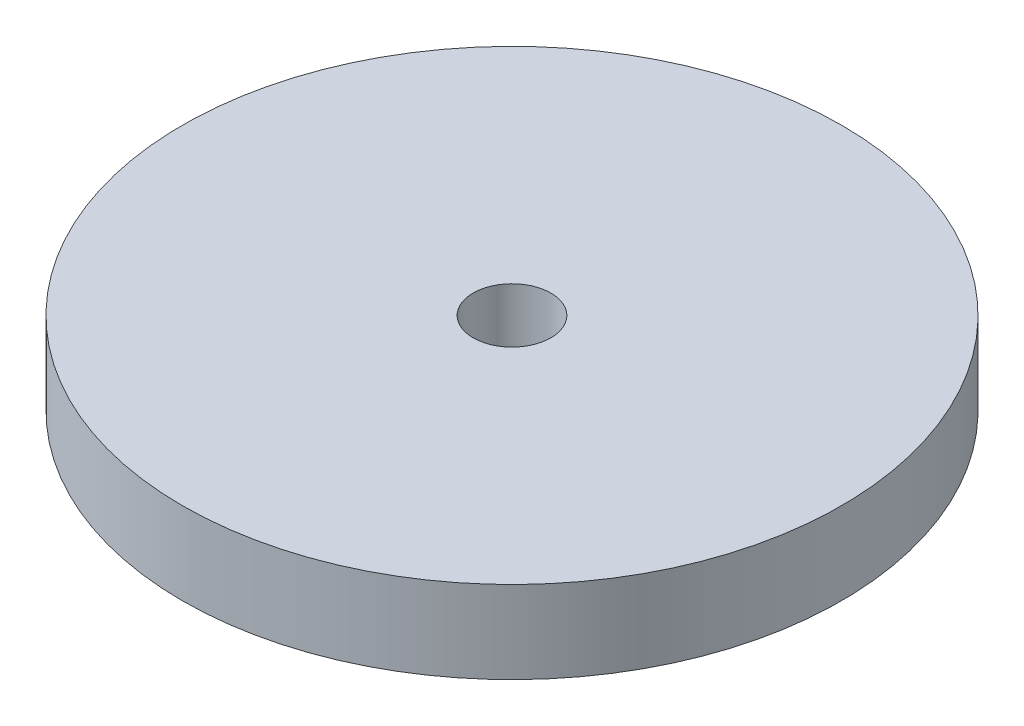
SolidWorks part; units mm, degrees
ref_plane "Front Plane" through (0, 0, 0) normal (0, 0, 1) x (1, 0, 0)
ref_plane "Top Plane" through (0, 0, 0) normal (0, 1, 0) x (1, 0, 0)
ref_plane "Right Plane" through (0, 0, 0) normal (1, 0, 0) x (0, 0, -1)
sketch "Sketch1" plane through (0, 0, 0) normal (0, 1, 0) x (1, 0, 0)
  circle A0 centre (0, 0) radius 14
  dimension "D1" = 28
extrude "Boss-Extrude1" add sketch "Sketch1" along normal blind 4
sketch "Sketch2" plane through (0, 0, 0) normal (0, -1, 0) x (1, 0, 0)
  circle A0 centre (0, 0) radius 6.5
  circle A1 centre (0, 0) radius 14
  dimension "D1" = 13
extrude "Cut-Extrude1" cut sketch "Sketch2" against normal blind 0.5
sketch "Sketch3" plane through (0, 4, 0) normal (0, 1, 0) x (1, 0, 0)
  circle A0 centre (0, 0) radius 1.65
  dimension "D1" = 3.3
extrude "Cut-Extrude2" cut sketch "Sketch3" against normal up to surface (4 mm away) up to face at (0, 0, -6.5)
